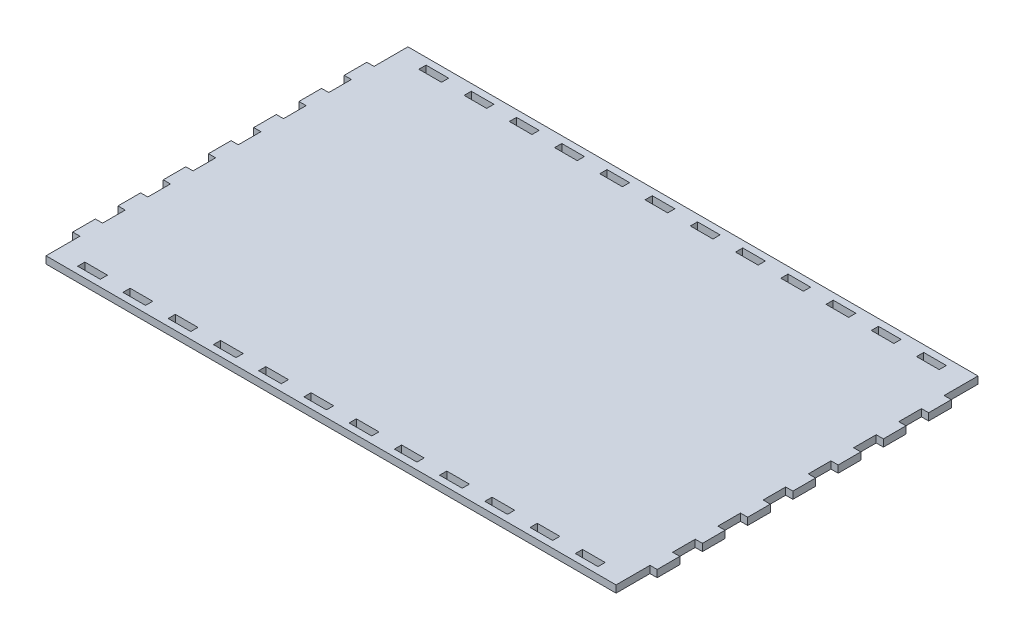
SolidWorks part; units mm, degrees
ref_plane "Front Plane" through (0, 0, 0) normal (0, 0, 1) x (1, 0, 0)
ref_plane "Top Plane" through (0, 0, 0) normal (0, 1, 0) x (1, 0, 0)
ref_plane "Right Plane" through (0, 0, 0) normal (1, 0, 0) x (0, 0, -1)
sketch "Sketch2" plane through (0, 0, 0) normal (0, 1, 0) x (1, 0, 0)
  line L0 (-137.6857, 51.9395) -> (-137.6857, 66.9395)
  line L1 (-137.6857, -93.0605) -> (114.3143, -93.0605)
  line L2 (-137.6857, -93.0605) -> (-137.6857, 66.9395) construction
  line L3 (-137.6857, 66.9395) -> (114.3143, 66.9395)
  line L4 (-106.6857, 63.9395) -> (-96.6857, 63.9395)
  line L5 (-140.8607, 51.9395) -> (-137.6857, 51.9395)
  line L6 (-140.8607, 51.9395) -> (-140.8607, 41.9395)
  line L7 (-140.8607, 41.9395) -> (-137.6857, 41.9395)
  line L8 (-137.6857, 21.9395) -> (-137.6857, 11.9395)
  line L9 (-137.6857, 31.9395) -> (-140.8607, 31.9395)
  line L10 (-137.6857, 1.9395) -> (-137.6857, -8.0605)
  line L11 (-137.6857, 21.9395) -> (-140.8607, 21.9395)
  line L12 (-140.8607, 31.9395) -> (-140.8607, 21.9395)
  line L13 (-137.6857, 11.9395) -> (-140.8607, 11.9395)
  line L14 (-137.6857, 1.9395) -> (-137.6857, -8.0605)
  line L15 (-137.6857, 1.9395) -> (-140.8607, 1.9395)
  line L16 (-140.8607, 11.9395) -> (-140.8607, 1.9395)
  line L17 (-137.6857, -8.0605) -> (-140.8607, -8.0605)
  line L18 (-140.8607, -8.0605) -> (-140.8607, -18.0605)
  line L19 (-137.6857, -13.0605) -> (-123.0659, -13.0605) construction
  line L20 (-137.6857, -78.0605) -> (-137.6857, -93.0605)
  line L21 (-137.6857, 41.9395) -> (-137.6857, 31.9395)
  line L22 (-140.8607, -78.0605) -> (-137.6857, -78.0605)
  line L23 (-140.8607, -68.0605) -> (-137.6857, -68.0605)
  line L24 (-137.6857, -58.0605) -> (-140.8607, -58.0605)
  line L25 (-137.6857, -68.0605) -> (-137.6857, -58.0605)
  line L26 (-137.6857, -38.0605) -> (-140.8607, -38.0605)
  line L27 (-137.6857, -48.0605) -> (-140.8607, -48.0605)
  line L28 (-137.6857, -48.0605) -> (-137.6857, -38.0605)
  line L29 (-137.6857, -18.0605) -> (-140.8607, -18.0605)
  line L30 (-137.6857, -28.0605) -> (-140.8607, -28.0605)
  line L31 (-137.6857, -28.0605) -> (-137.6857, -18.0605)
  line L32 (-140.8607, -38.0605) -> (-140.8607, -28.0605)
  line L33 (-140.8607, -58.0605) -> (-140.8607, -48.0605)
  line L34 (-140.8607, -78.0605) -> (-140.8607, -68.0605)
  line L35 (-11.6857, 56.9395) -> (-11.6857, -157.3988) construction
  line L36 (117.4893, -78.0605) -> (117.4893, -68.0605)
  line L37 (117.4893, -58.0605) -> (117.4893, -48.0605)
  line L38 (117.4893, -38.0605) -> (117.4893, -28.0605)
  line L39 (114.3143, -28.0605) -> (114.3143, -18.0605)
  line L40 (114.3143, -28.0605) -> (117.4893, -28.0605)
  line L41 (114.3143, -18.0605) -> (117.4893, -18.0605)
  line L42 (114.3143, -48.0605) -> (114.3143, -38.0605)
  line L43 (114.3143, -48.0605) -> (117.4893, -48.0605)
  line L44 (114.3143, -38.0605) -> (117.4893, -38.0605)
  line L45 (114.3143, -68.0605) -> (114.3143, -58.0605)
  line L46 (114.3143, -58.0605) -> (117.4893, -58.0605)
  line L47 (117.4893, -68.0605) -> (114.3143, -68.0605)
  line L48 (117.4893, -78.0605) -> (114.3143, -78.0605)
  line L49 (114.3143, 41.9395) -> (114.3143, 31.9395)
  line L50 (114.3143, -78.0605) -> (114.3143, -93.0605)
  line L51 (117.4893, -8.0605) -> (117.4893, -18.0605)
  line L52 (114.3143, -8.0605) -> (117.4893, -8.0605)
  line L53 (117.4893, 11.9395) -> (117.4893, 1.9395)
  line L54 (114.3143, 1.9395) -> (117.4893, 1.9395)
  line L55 (114.3143, 1.9395) -> (114.3143, -8.0605)
  line L56 (114.3143, 11.9395) -> (117.4893, 11.9395)
  line L57 (117.4893, 31.9395) -> (117.4893, 21.9395)
  line L58 (114.3143, 21.9395) -> (117.4893, 21.9395)
  line L59 (114.3143, 1.9395) -> (114.3143, -8.0605)
  line L60 (114.3143, 31.9395) -> (117.4893, 31.9395)
  line L61 (114.3143, 21.9395) -> (114.3143, 11.9395)
  line L62 (117.4893, 41.9395) -> (114.3143, 41.9395)
  line L63 (117.4893, 51.9395) -> (117.4893, 41.9395)
  line L64 (117.4893, 51.9395) -> (114.3143, 51.9395)
  line L65 (114.3143, 51.9395) -> (114.3143, 66.9395)
  line L70 (-126.6857, 63.9395) -> (-116.6857, 63.9395)
  line L71 (-126.6857, 63.9395) -> (-126.6857, 60.7645)
  line L72 (-126.6857, 60.7645) -> (-116.6857, 60.7645)
  line L73 (-116.6857, 63.9395) -> (-116.6857, 60.7645)
  line L74 (-106.6857, 63.9395) -> (-106.6857, 60.7645)
  line L75 (-106.6857, 60.7645) -> (-96.6857, 60.7645)
  line L76 (-96.6857, 63.9395) -> (-96.6857, 60.7645)
  line L77 (-86.6857, 63.9395) -> (-76.6857, 63.9395)
  line L78 (-86.6857, 63.9395) -> (-86.6857, 60.7645)
  line L79 (-86.6857, 60.7645) -> (-76.6857, 60.7645)
  line L80 (-76.6857, 63.9395) -> (-76.6857, 60.7645)
  line L81 (-66.6857, 63.9395) -> (-56.6857, 63.9395)
  line L82 (-66.6857, 63.9395) -> (-66.6857, 60.7645)
  line L83 (-66.6857, 60.7645) -> (-56.6857, 60.7645)
  line L84 (-56.6857, 63.9395) -> (-56.6857, 60.7645)
  line L85 (-46.6857, 63.9395) -> (-36.6857, 63.9395)
  line L86 (-46.6857, 63.9395) -> (-46.6857, 60.7645)
  line L87 (-46.6857, 60.7645) -> (-36.6857, 60.7645)
  line L88 (-36.6857, 63.9395) -> (-36.6857, 60.7645)
  line L89 (-26.6857, 63.9395) -> (-16.6857, 63.9395)
  line L90 (-26.6857, 63.9395) -> (-26.6857, 60.7645)
  line L91 (-26.6857, 60.7645) -> (-16.6857, 60.7645)
  line L92 (-16.6857, 63.9395) -> (-16.6857, 60.7645)
  line L93 (-6.6857, 63.9395) -> (3.3143, 63.9395)
  line L94 (-6.6857, 63.9395) -> (-6.6857, 60.7645)
  line L95 (-6.6857, 60.7645) -> (3.3143, 60.7645)
  line L96 (3.3143, 63.9395) -> (3.3143, 60.7645)
  line L97 (13.3143, 63.9395) -> (23.3143, 63.9395)
  line L98 (13.3143, 63.9395) -> (13.3143, 60.7645)
  line L99 (13.3143, 60.7645) -> (23.3143, 60.7645)
  line L100 (23.3143, 63.9395) -> (23.3143, 60.7645)
  line L101 (33.3143, 63.9395) -> (43.3143, 63.9395)
  line L102 (33.3143, 63.9395) -> (33.3143, 60.7645)
  line L103 (33.3143, 60.7645) -> (43.3143, 60.7645)
  line L104 (43.3143, 63.9395) -> (43.3143, 60.7645)
  line L105 (53.3143, 63.9395) -> (63.3143, 63.9395)
  line L106 (53.3143, 63.9395) -> (53.3143, 60.7645)
  line L107 (53.3143, 60.7645) -> (63.3143, 60.7645)
  line L108 (63.3143, 63.9395) -> (63.3143, 60.7645)
  line L109 (73.3143, 63.9395) -> (83.3143, 63.9395)
  line L110 (73.3143, 63.9395) -> (73.3143, 60.7645)
  line L111 (73.3143, 60.7645) -> (83.3143, 60.7645)
  line L112 (83.3143, 63.9395) -> (83.3143, 60.7645)
  line L113 (93.3143, 63.9395) -> (103.3143, 63.9395)
  line L114 (93.3143, 63.9395) -> (93.3143, 60.7645)
  line L115 (93.3143, 60.7645) -> (103.3143, 60.7645)
  line L116 (103.3143, 63.9395) -> (103.3143, 60.7645)
  line L117 (-126.6857, 63.9395) -> (-106.6857, 63.9395) construction
  line L118 (-126.6857, -90.0605) -> (-106.6857, -90.0605) construction
  line L119 (103.3143, -90.0605) -> (103.3143, -86.8855)
  line L120 (93.3143, -86.8855) -> (103.3143, -86.8855)
  line L121 (93.3143, -90.0605) -> (93.3143, -86.8855)
  line L122 (93.3143, -90.0605) -> (103.3143, -90.0605)
  line L123 (83.3143, -90.0605) -> (83.3143, -86.8855)
  line L124 (73.3143, -86.8855) -> (83.3143, -86.8855)
  line L125 (73.3143, -90.0605) -> (73.3143, -86.8855)
  line L126 (73.3143, -90.0605) -> (83.3143, -90.0605)
  line L127 (63.3143, -90.0605) -> (63.3143, -86.8855)
  line L128 (53.3143, -86.8855) -> (63.3143, -86.8855)
  line L129 (53.3143, -90.0605) -> (53.3143, -86.8855)
  line L130 (53.3143, -90.0605) -> (63.3143, -90.0605)
  line L131 (43.3143, -90.0605) -> (43.3143, -86.8855)
  line L132 (33.3143, -86.8855) -> (43.3143, -86.8855)
  line L133 (33.3143, -90.0605) -> (33.3143, -86.8855)
  line L134 (33.3143, -90.0605) -> (43.3143, -90.0605)
  line L135 (23.3143, -90.0605) -> (23.3143, -86.8855)
  line L136 (13.3143, -86.8855) -> (23.3143, -86.8855)
  line L137 (13.3143, -90.0605) -> (13.3143, -86.8855)
  line L138 (13.3143, -90.0605) -> (23.3143, -90.0605)
  line L139 (3.3143, -90.0605) -> (3.3143, -86.8855)
  line L140 (-6.6857, -86.8855) -> (3.3143, -86.8855)
  line L141 (-6.6857, -90.0605) -> (-6.6857, -86.8855)
  line L142 (-6.6857, -90.0605) -> (3.3143, -90.0605)
  line L143 (-16.6857, -90.0605) -> (-16.6857, -86.8855)
  line L144 (-26.6857, -86.8855) -> (-16.6857, -86.8855)
  line L145 (-26.6857, -90.0605) -> (-26.6857, -86.8855)
  line L146 (-26.6857, -90.0605) -> (-16.6857, -90.0605)
  line L147 (-36.6857, -90.0605) -> (-36.6857, -86.8855)
  line L148 (-46.6857, -86.8855) -> (-36.6857, -86.8855)
  line L149 (-46.6857, -90.0605) -> (-46.6857, -86.8855)
  line L150 (-46.6857, -90.0605) -> (-36.6857, -90.0605)
  line L151 (-56.6857, -90.0605) -> (-56.6857, -86.8855)
  line L152 (-66.6857, -86.8855) -> (-56.6857, -86.8855)
  line L153 (-66.6857, -90.0605) -> (-66.6857, -86.8855)
  line L154 (-66.6857, -90.0605) -> (-56.6857, -90.0605)
  line L155 (-76.6857, -90.0605) -> (-76.6857, -86.8855)
  line L156 (-86.6857, -86.8855) -> (-76.6857, -86.8855)
  line L157 (-86.6857, -90.0605) -> (-86.6857, -86.8855)
  line L158 (-86.6857, -90.0605) -> (-76.6857, -90.0605)
  line L159 (-96.6857, -90.0605) -> (-96.6857, -86.8855)
  line L160 (-106.6857, -86.8855) -> (-96.6857, -86.8855)
  line L161 (-106.6857, -90.0605) -> (-106.6857, -86.8855)
  line L162 (-116.6857, -90.0605) -> (-116.6857, -86.8855)
  line L163 (-126.6857, -86.8855) -> (-116.6857, -86.8855)
  line L164 (-126.6857, -90.0605) -> (-126.6857, -86.8855)
  line L165 (-126.6857, -90.0605) -> (-116.6857, -90.0605)
  line L166 (-106.6857, -90.0605) -> (-96.6857, -90.0605)
  point P8 (-139.2732, 51.9395)
  point P17 (-139.2732, 11.9395)
  point P37 (-140.8607, -13.0605)
  point P67 (117.4893, -13.0605)
  dimension "D1" = 252
  dimension "D2" = 3.175
  dimension "D3" = 10
  dimension "D4" = 15
  dimension "D5" = 10
  dimension "D6" = 3.175
  dimension "D7" = 10
  dimension "D8" = 10
  dimension "D9" = 3.175
  dimension "D10" = 10
  dimension "D11" = 10
  dimension "D12" = 3.175
  dimension "D13" = 5
  dimension "D22" = 10
  dimension "D23" = 3.175
  dimension "D24" = 11
  dimension "D25" = 3
  dimension "D26" = 20
  dimension "D27" = 11
extrude "Boss-Extrude1" add sketch "Sketch2" along normal blind 3.175 contours L64 L65 L3 L0 L5 L6 L7 L21 L9 L12 L11 L8 L13 L16 L15 L10 L17 L18 L29 L31 L30 L32 L26 L28 L27 L33 L24 L25 L23 L34 L22 L20 L1 L50 L48 L36 L47 L45 L46 L37 L43 L42 L44 L38 L40 L39 L41 L51 L52 L55 L54
